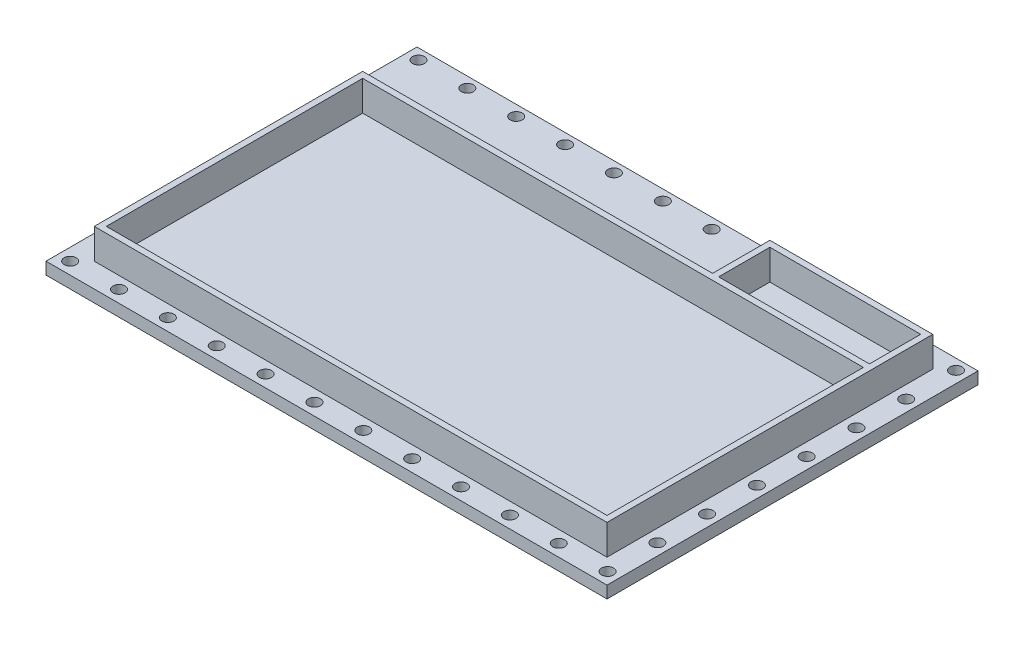
SolidWorks part; units mm, degrees
ref_plane "Front Plane" through (0, 0, 0) normal (0, 0, 1) x (1, 0, 0)
ref_plane "Top Plane" through (0, 0, 0) normal (0, 1, 0) x (1, 0, 0)
ref_plane "Right Plane" through (0, 0, 0) normal (1, 0, 0) x (0, 0, -1)
sketch "Sketch1" plane through (0, 0, 0) normal (0, 1, 0) x (1, 0, 0)
  line L0 (0, 89) -> (116, 89)
  line L1 (0, 0) -> (170, 0)
  line L2 (0, 0) -> (0, 89)
  line L4 (170, 0) -> (170, 89)
  line L9 (2, 2) -> (168, 2)
  line L10 (2, 2) -> (2, 87)
  line L11 (2, 87) -> (168, 87)
  line L12 (168, 2) -> (168, 87)
  line L15 (170, 108) -> (116, 108)
  line L16 (116, 89) -> (116, 108)
  line L21 (168, 89) -> (118, 89)
  line L22 (168, 89) -> (168, 106)
  line L23 (168, 106) -> (118, 106)
  line L24 (118, 89) -> (118, 106)
  line L25 (170, 108) -> (170, 89)
extrude "Boss-Extrude4" add sketch "Sketch1" along normal blind 10
sketch "Sketch2" plane through (0, 0, 0) normal (0, -1, 0) x (1, 0, 0)
  line L9 (-8, 8) -> (178, 8)
  line L10 (-8, 8) -> (-8, -115)
  line L11 (-8, -115) -> (178, -115)
  line L12 (178, 8) -> (178, -115)
extrude "Boss-Extrude5" add sketch "Sketch2" along normal blind 4
sketch "Sketch3" plane through (0, 0, 0) normal (0, 1, 0) x (1, 0, 0)
  circle A0 centre (-4, -4) radius 2
  circle A1 centre (12.2, -4) radius 2
  circle A2 centre (28.4, -4) radius 2
  circle A3 centre (44.6, -4) radius 2
  circle A4 centre (60.8, -4) radius 2
  circle A5 centre (77, -4) radius 2
  circle A6 centre (93.2, -4) radius 2
  circle A7 centre (109.4, -4) radius 2
  circle A8 centre (125.6, -4) radius 2
  circle A9 centre (141.8, -4) radius 2
  circle A10 centre (158, -4) radius 2
  circle A11 centre (174.2, -4) radius 2
  circle A22 centre (174.2, 12.5) radius 2
  circle A33 centre (174.2, 29) radius 2
  circle A44 centre (174.2, 45.5) radius 2
  circle A55 centre (174.2, 62) radius 2
  circle A66 centre (174.2, 78.5) radius 2
  circle A77 centre (174.2, 95) radius 2
  circle A78 centre (12.2, 111.5) radius 2
  circle A79 centre (28.4, 111.5) radius 2
  circle A80 centre (44.6, 111.5) radius 2
  circle A81 centre (60.8, 111.5) radius 2
  circle A82 centre (77, 111.5) radius 2
  circle A83 centre (93.2, 111.5) radius 2
  circle A84 centre (109.4, 111.5) radius 2
  circle A85 centre (125.6, 111.5) radius 2
  circle A86 centre (141.8, 111.5) radius 2
  circle A87 centre (158, 111.5) radius 2
  circle A88 centre (174.2, 111.5) radius 2
  circle A89 centre (-4, 12.5) radius 2
  circle A90 centre (-4, 29) radius 2
  circle A91 centre (-4, 45.5) radius 2
  circle A92 centre (-4, 62) radius 2
  circle A93 centre (-4, 78.5) radius 2
  circle A94 centre (-4, 95) radius 2
  circle A95 centre (-4, 111.5) radius 2
  circle A96 centre (12.2, 12.5) radius 2 [skipped]
  circle A97 centre (28.4, 12.5) radius 2 [skipped]
  circle A98 centre (44.6, 12.5) radius 2 [skipped]
  circle A99 centre (60.8, 12.5) radius 2 [skipped]
  circle A100 centre (77, 12.5) radius 2 [skipped]
  circle A101 centre (93.2, 12.5) radius 2 [skipped]
  circle A102 centre (109.4, 12.5) radius 2 [skipped]
  circle A103 centre (125.6, 12.5) radius 2 [skipped]
  circle A104 centre (141.8, 12.5) radius 2 [skipped]
  circle A105 centre (158, 12.5) radius 2 [skipped]
  circle A106 centre (12.2, 29) radius 2 [skipped]
  circle A107 centre (28.4, 29) radius 2 [skipped]
  circle A108 centre (44.6, 29) radius 2 [skipped]
  circle A109 centre (60.8, 29) radius 2 [skipped]
  circle A110 centre (77, 29) radius 2 [skipped]
  circle A111 centre (93.2, 29) radius 2 [skipped]
  circle A112 centre (109.4, 29) radius 2 [skipped]
  circle A113 centre (125.6, 29) radius 2 [skipped]
  circle A114 centre (141.8, 29) radius 2 [skipped]
  circle A115 centre (158, 29) radius 2 [skipped]
  circle A116 centre (12.2, 45.5) radius 2 [skipped]
  circle A117 centre (28.4, 45.5) radius 2 [skipped]
  circle A118 centre (44.6, 45.5) radius 2 [skipped]
  circle A119 centre (60.8, 45.5) radius 2 [skipped]
  circle A120 centre (77, 45.5) radius 2 [skipped]
  circle A121 centre (93.2, 45.5) radius 2 [skipped]
  circle A122 centre (109.4, 45.5) radius 2 [skipped]
  circle A123 centre (125.6, 45.5) radius 2 [skipped]
  circle A124 centre (141.8, 45.5) radius 2 [skipped]
  circle A125 centre (158, 45.5) radius 2 [skipped]
  circle A126 centre (12.2, 62) radius 2 [skipped]
  circle A127 centre (28.4, 62) radius 2 [skipped]
  circle A128 centre (44.6, 62) radius 2 [skipped]
  circle A129 centre (60.8, 62) radius 2 [skipped]
  circle A130 centre (77, 62) radius 2 [skipped]
  circle A131 centre (93.2, 62) radius 2 [skipped]
  circle A132 centre (109.4, 62) radius 2 [skipped]
  circle A133 centre (125.6, 62) radius 2 [skipped]
  circle A134 centre (141.8, 62) radius 2 [skipped]
  circle A135 centre (158, 62) radius 2 [skipped]
  circle A136 centre (12.2, 78.5) radius 2 [skipped]
  circle A137 centre (28.4, 78.5) radius 2 [skipped]
  circle A138 centre (44.6, 78.5) radius 2 [skipped]
  circle A139 centre (60.8, 78.5) radius 2 [skipped]
  circle A140 centre (77, 78.5) radius 2 [skipped]
  circle A141 centre (93.2, 78.5) radius 2 [skipped]
  circle A142 centre (109.4, 78.5) radius 2 [skipped]
  circle A143 centre (125.6, 78.5) radius 2 [skipped]
  circle A144 centre (141.8, 78.5) radius 2 [skipped]
  circle A145 centre (158, 78.5) radius 2 [skipped]
  circle A146 centre (12.2, 95) radius 2 [skipped]
  circle A147 centre (28.4, 95) radius 2 [skipped]
  circle A148 centre (44.6, 95) radius 2 [skipped]
  circle A149 centre (60.8, 95) radius 2 [skipped]
  circle A150 centre (77, 95) radius 2 [skipped]
  circle A151 centre (93.2, 95) radius 2 [skipped]
  circle A152 centre (109.4, 95) radius 2 [skipped]
  circle A153 centre (125.6, 95) radius 2 [skipped]
  circle A154 centre (141.8, 95) radius 2 [skipped]
  circle A155 centre (158, 95) radius 2 [skipped]
  dimension "D1" = 12
  dimension "D2" = 8
extrude "Cut-Extrude2" cut sketch "Sketch3" against normal blind 4
